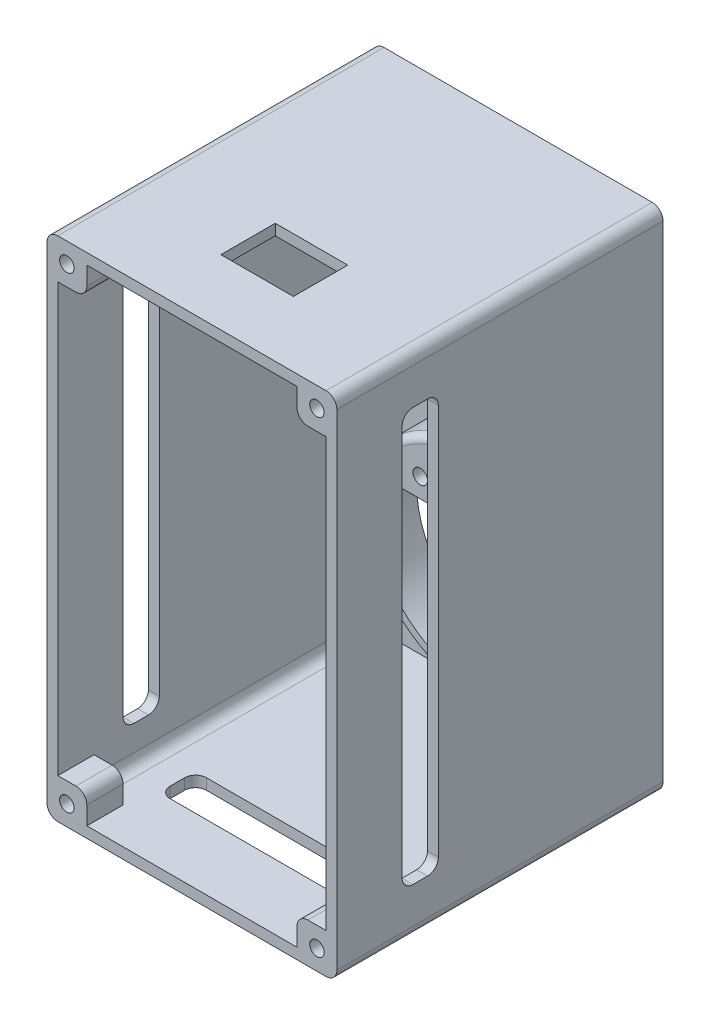
SolidWorks part; units mm, degrees
ref_plane "Front Plane" through (0, 0, 0) normal (0, 0, 1) x (1, 0, 0)
ref_plane "Top Plane" through (0, 0, 0) normal (0, 1, 0) x (1, 0, 0)
ref_plane "Right Plane" through (0, 0, 0) normal (1, 0, 0) x (0, 0, -1)
sketch "Sketch1" plane through (0, 0, 0) normal (0, 1, 0) x (1, 0, 0)
  line L1 (0, 0) -> (80, 0)
  line L2 (0, 0) -> (0, 80)
  line L3 (0, 80) -> (80, 80)
  line L4 (80, 0) -> (80, 80)
  dimension "D1" = 80
  dimension "D2" = 80
extrude "Boss-Extrude1" add sketch "Sketch1" along normal blind 80
shell "Shell1" thickness 3
sketch "Sketch2" plane through (0, 0, -80) normal (0, 0, -1) x (-1, 0, 0)
  line L0 (0, 40) -> (-49.5068, 40) construction
  line L1 (0, 80) -> (0, 0) construction
  line L2 (-40, 80) -> (-40, 29.0951) construction
  line L3 (-80, 80) -> (0, 80) construction
  circle A0 centre (-40, 40) radius 27
  dimension "D1" = 54
extrude "Cut-Extrude1" cut sketch "Sketch2" against normal up to next
sketch "Sketch3" plane through (0, 0, -77) normal (0, 0, 1) x (1, 0, 0)
  circle A0 centre (40, 40) radius 30
  circle A1 centre (40, 40) radius 27 construction
  circle A2 centre (40, 40) radius 27
  dimension "D1" = 3
extrude "Boss-Extrude2" add sketch "Sketch3" along normal blind 9
sketch "Sketch4" plane through (0, 0, -68) normal (0, 0, 1) x (1, 0, 0)
  line L0 (40, 40) -> (40, 26.1871) construction
  line L4 (18, 60.3961) -> (18, 19.6039)
  line L5 (62, 60.3961) -> (62, 19.6039)
  arc A0 (18, 60.3961) -> (18, 19.6039) centre (40, 40) ccw
  arc A1 (62, 60.3961) -> (62, 19.6039) centre (40, 40) cw
  dimension "D1" = 22
  dimension "D2" = 30
extrude "Boss-Extrude3" add sketch "Sketch4" along normal blind 3
sketch "Sketch5" plane through (0, 0, 0) normal (0, -1, 0) x (1, 0, 0)
  line L1 (0, 0) -> (104.1991, 0)
  line L2 (0, 0) -> (0, -10)
  line L3 (0, -10) -> (104.1991, -10)
  line L4 (104.1991, 0) -> (104.1991, -10)
  dimension "D1" = 10
extrude "Cut-Extrude2" cut sketch "Sketch5" against normal through all both and the other way through all
sketch "Sketch8" plane through (0, 0, -68) normal (0, 0, 1) x (1, 0, 0)
  line L2 (18, 60.3961) -> (18, 52.1352)
  line L3 (18, 52.1352) -> (62, 52.1352)
  line L4 (62, 60.3961) -> (62, 52.1352)
  arc A0 (62, 60.3961) -> (18, 60.3961) centre (40, 40) ccw
extrude "Boss-Extrude4" add sketch "Sketch8" along normal up to surface (3 mm away) up to face at (14, 40, -65)
fillet "Fillet3" radius 3 2 edges at (62, 52.1352, -66.5) (18, 52.1352, -66.5)
fillet "Fillet4" radius 2 1 edges at (40, 70, -65)
sketch "Sketch9" plane through (0, 0, -68) normal (0, 0, -1) x (-1, 0, 0)
  circle A0 centre (-52, 57.5) radius 2
  circle A1 centre (-28, 57.5) radius 2
  circle A2 centre (-40, 40) radius 27 construction
  arc A3 (-18, 24.3475) -> (-62, 24.3475) centre (-40, 40) ccw construction
  dimension "D1" = 17.5
  dimension "D2" = 12
  dimension "D3" = 17.5
  dimension "D4" = 12
  dimension "D5" = 4
  dimension "D6" = 4
extrude "Cut-Extrude5" cut sketch "Sketch9" against normal up to next
sketch "Sketch13" plane through (0, 0, -80) normal (0, 0, -1) x (-1, 0, 0)
  line L1 (-80, 80) -> (0, 80)
  line L2 (-80, 80) -> (-80, 140)
  line L3 (-80, 140) -> (0, 140)
  line L4 (0, 80) -> (0, 140)
  dimension "D1" = 60
extrude "Boss-Extrude6" add sketch "Sketch13" against normal up to surface (70 mm away) up to face at (40, 40, -10)
sketch "Sketch14" plane through (0, 0, -10) normal (0, 0, 1) x (1, 0, 0)
  line L0 (80, 140) -> (80, 0) construction
  line L1 (3, 77) -> (77, 77)
  line L2 (3, 77) -> (3, 137)
  line L3 (3, 137) -> (77, 137)
  line L4 (77, 77) -> (77, 137)
  line L5 (80, 140) -> (0, 140) construction
  dimension "D1" = 3
  dimension "D2" = 3
extrude "Cut-Extrude8" cut sketch "Sketch14" against normal up to surface (67 mm away) up to face at (40, 40, -77)
sketch "Sketch15" plane through (0, 0, -10) normal (0, 0, 1) x (1, 0, 0)
  line L1 (0, 0) -> (80, 0)
  line L2 (0, 0) -> (0, 140)
  line L3 (0, 140) -> (80, 140)
  line L4 (80, 0) -> (80, 140)
  line L5 (3, 137) -> (77, 137)
  line L6 (3, 137) -> (3, 3)
  line L7 (3, 3) -> (77, 3)
  line L8 (77, 137) -> (77, 3)
extrude "Boss-Extrude7" add sketch "Sketch15" along normal blind 20
sketch "Sketch12" plane through (0, 0, -80) normal (0, 0, -1) x (-1, 0, 0)
  circle A0 centre (-40, 40) radius 28
  arc A1 (-18, 24.3475) -> (-62, 24.3475) centre (-40, 40) ccw construction
  dimension "D1" = 1
extrude "Cut-Extrude7" cut sketch "Sketch12" against normal up to surface (12 mm away) up to face at (50, 57.5, -68)
fillet "Fillet5" radius 3 8 edges at (80, 140, -35) (0, 140, -35) (3, 137, -33.5) (77, 137, -33.5) (3, 3, -33.5) (77, 3, -33.5) (0, 0, -35) (80, 0, -35)
sketch "Sketch16" plane through (0, 0, 10) normal (0, 0, 1) x (1, 0, 0)
  line L0 (6, 3) -> (74, 3) construction
  line L1 (1.8865, 1.516) -> (11, 1.516)
  line L2 (1.8865, 1.516) -> (1.8865, 11)
  line L3 (1.8865, 11) -> (11, 11)
  line L4 (11, 1.516) -> (11, 11)
  line L5 (3, 134) -> (3, 6) construction
  line L6 (77, 134) -> (77, 6) construction
  line L7 (77, 3) -> (69, 3)
  line L8 (77, 3) -> (77, 11)
  line L9 (77, 11) -> (69, 11)
  line L10 (69, 3) -> (69, 11)
  line L11 (74, 137) -> (6, 137) construction
  line L12 (77, 137) -> (69, 137)
  line L13 (77, 137) -> (77, 129)
  line L14 (77, 129) -> (69, 129)
  line L15 (69, 137) -> (69, 129)
  line L16 (3, 137) -> (11, 137)
  line L17 (3, 137) -> (3, 129)
  line L18 (3, 129) -> (11, 129)
  line L19 (11, 137) -> (11, 129)
  dimension "D1" = 8
  dimension "D2" = 8
  dimension "D3" = 8
  dimension "D4" = 8
  dimension "D5" = 8
  dimension "D6" = 8
  dimension "D7" = 8
  dimension "D8" = 8
extrude "Boss-Extrude8" add sketch "Sketch16" against normal blind 10
sketch "Sketch17" plane through (0, 0, 0) normal (-1, 0, 0) x (0, 0, 1)
  line L0 (10, 137) -> (-80, 137) construction
  line L1 (-18, 127) -> (-8, 127)
  line L2 (-18, 127) -> (-18, 13)
  line L3 (-18, 13) -> (-8, 13)
  line L4 (-8, 127) -> (-8, 13)
  line L5 (-80, 3) -> (10, 3) construction
  line L6 (10, 137) -> (10, 3) construction
  dimension "D1" = 10
  dimension "D2" = 10
  dimension "D3" = 18
  dimension "D4" = 10
extrude "Cut-Extrude9" cut sketch "Sketch17" against normal through all
sketch "Sketch18" plane through (0, 140, 0) normal (0, 1, 0) x (1, 0, 0)
  line L0 (77, -10) -> (77, 80) construction
  line L1 (13, 18) -> (67, 18)
  line L2 (13, 18) -> (13, 8)
  line L3 (13, 8) -> (67, 8)
  line L4 (67, 18) -> (67, 8)
  line L5 (3, 80) -> (3, -10) construction
  line L6 (77, -10) -> (3, -10) construction
  dimension "D1" = 10
  dimension "D2" = 10
  dimension "D3" = 18
  dimension "D4" = 10
extrude "Cut-Extrude10" cut sketch "Sketch18" against normal through all from offset 10 offset against normal yes
fillet "Fillet6" radius 3 12 edges at (78.5, 13, -18) (78.5, 13, -8) (78.5, 127, -18) (78.5, 127, -8) (67, 1.5, -18) (67, 1.5, -8) (13, 1.5, -8) (13, 1.5, -18) (1.5, 127, -8) (1.5, 127, -18) (1.5, 13, -8) (1.5, 13, -18)
sketch "Sketch19" plane through (0, 0, 10) normal (0, 0, 1) x (1, 0, 0)
  line L0 (0, 137) -> (0, 3) construction
  line L1 (77, 140) -> (3, 140) construction
  line L2 (0, 70) -> (63.0063, 70) construction
  line L3 (40, 140) -> (40, 30.2768) construction
  circle A0 centre (5.5, 134.5) radius 2
  circle A1 centre (74.5, 134.5) radius 2
  circle A2 centre (74.5, 5.5) radius 2
  circle A3 centre (5.5, 5.5) radius 2
  dimension "D1" = 4
  dimension "D2" = 5.5
  dimension "D3" = 5.5
extrude "Cut-Extrude11" cut sketch "Sketch19" against normal up to next
fillet "Fillet7" radius 3 4 edges at (11, 11, 5) (69, 11, 5) (69, 129, 5) (11, 129, 5)
sketch "Sketch20" plane through (0, 140, 0) normal (0, 1, 0) x (1, 0, 0)
  line L0 (40, -10) -> (40, 35.3146) construction
  line L1 (30, 23) -> (50, 23)
  line L2 (30, 23) -> (30, 8)
  line L3 (30, 8) -> (50, 8)
  line L4 (50, 23) -> (50, 8)
  line L5 (77, -10) -> (3, -10) construction
  dimension "D1" = 15
  dimension "D2" = 20
  dimension "D3" = 10
  dimension "D4" = 18
extrude "Cut-Extrude12" cut sketch "Sketch20" against normal up to next
